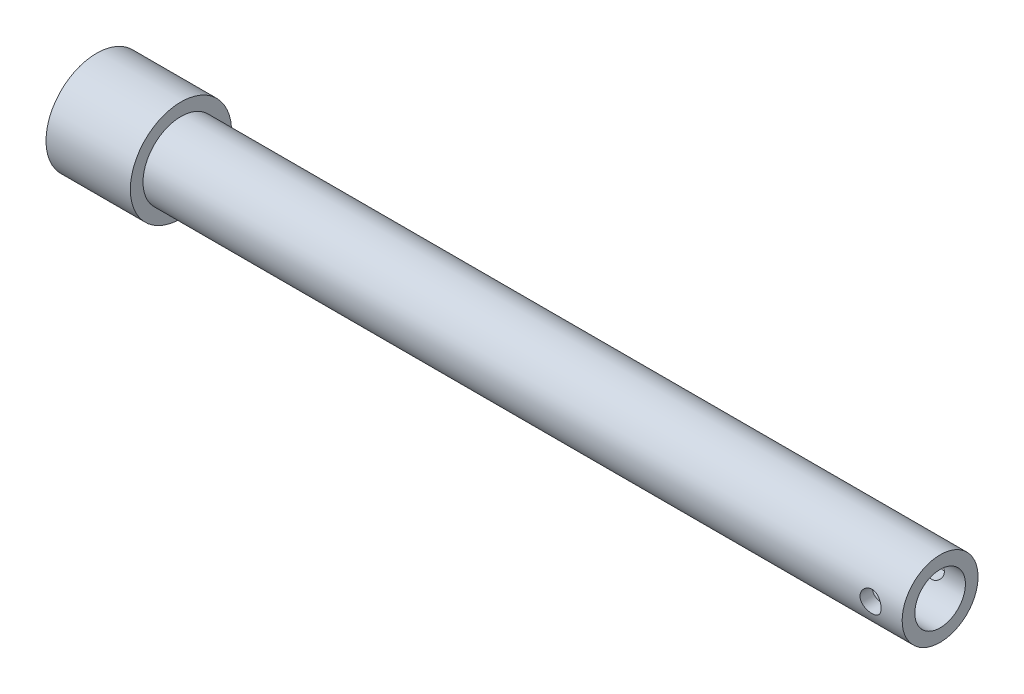
SolidWorks part; units mm, degrees
ref_plane "Front Plane" through (0, 0, 0) normal (0, 0, 1) x (1, 0, 0)
ref_plane "Top Plane" through (0, 0, 0) normal (0, 1, 0) x (1, 0, 0)
ref_plane "Right Plane" through (0, 0, 0) normal (1, 0, 0) x (0, 0, -1)
sketch "Sketch1" plane through (0, 0, 0) normal (0, 0, 1) x (1, 0, 0)
  line L1 (0, 0) -> (20, 0)
  line L2 (0, 0) -> (0, -12)
  line L3 (20, -9) -> (200, -9)
  line L4 (200, -6) -> (200, -9)
  line L7 (0, -12) -> (20, -12)
  line L8 (20, -9) -> (20, -12)
  line L10 (20, 0) -> (20, -6)
  line L11 (20, -6) -> (200, -6)
  dimension "D1" = 12
  dimension "D2" = 3
  dimension "D3" = 3
  dimension "D4" = 20
  dimension "D5" = 200
revolve "Revolve1" add sketch "Sketch1" angle 360 about L1
sketch "Sketch2" plane through (0, 0, 0) normal (0, 0, 1) x (1, 0, 0)
  line L0 (200, -9) -> (200, 9) construction
  line L1 (55, 0) -> (-55, 0) construction
  circle A0 centre (192.5, 0) radius 2.5
  dimension "D1" = 5
  dimension "D2" = 7.5
extrude "Cut-Extrude1" cut sketch "Sketch2" against normal through all both and the other way through all contours A0
sketch "Sketch3" plane through (0, 0, 0) normal (-1, 0, 0) x (0, 0, 1)
  point P0 (0, 0)
